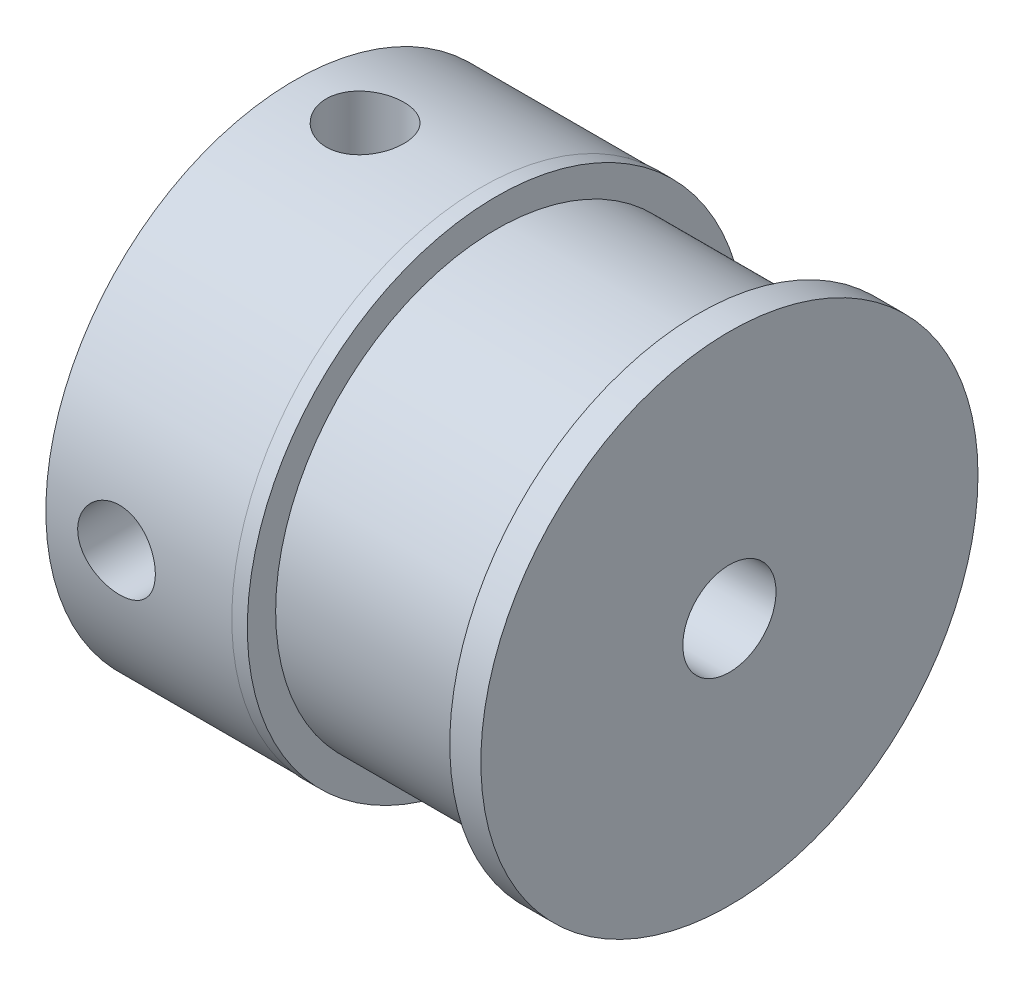
SolidWorks part; units mm, degrees
material "6061-T6 (SS)"
ref_plane "Front Plane" through (0, 0, 0) normal (0, 0, 1) x (1, 0, 0)
ref_plane "Top Plane" through (0, 0, 0) normal (0, 1, 0) x (1, 0, 0)
ref_plane "Right Plane" through (0, 0, 0) normal (1, 0, 0) x (0, 0, -1)
sketch "Sketch1" plane through (0, 0, 0) normal (0, 0, 1) x (1, 0, 0)
  line L0 (1.4515, 1.5) -> (1.4515, 8)
  line L1 (7.4515, 8.0157) -> (7.9515, 8.0157)
  line L2 (7.9515, 8.0157) -> (7.9515, 7.104)
  line L3 (7.9515, 7.104) -> (14.4515, 7.104)
  line L4 (14.4515, 7.104) -> (14.4515, 8)
  line L5 (14.4515, 8) -> (15.4515, 8)
  line L6 (15.4515, 8) -> (15.4515, 1.5)
  line L7 (15.4515, 1.5) -> (1.4515, 1.5)
  line L8 (0, 0) -> (-7.6744, 0) construction
  line L9 (7.4515, 8.0157) -> (7.4515, 8)
  line L10 (7.4515, 8) -> (1.4515, 8)
  point P1 (7.4515, 9.4661)
  dimension "D1" = 6.5
  dimension "D2" = 6.5
  dimension "D3" = 1.5
  dimension "D5" = 14
  dimension "D6" = 1
revolve "Revolve1" add sketch "Sketch1" angle 360 about L8
hole_wizard "M3x0.5 Tapped Hole1" positions "Sketch3" profile "Sketch2" tap size "M3x0.5" standard "ANSI Metric"
sketch "Sketch3" plane through (0, 0, 0) normal (0, 1, 0) x (1, 0, 0)
  line L0 (0, 0) -> (7.4515, 0) construction
  line L2 (7.4515, 8) -> (7.4515, -8) construction
  point P8 (3.7257, 0)
sketch "Sketch2" plane through (3.7257, 0, 0) normal (1, 0, 0) x (0, 0, -1)
  line L0 (0, 0) -> (0, 8.0157)
  line L1 (0, 8.0157) -> (1.25, 8.0157)
  line L2 (1.25, 8.0157) -> (1.25, 0)
  line L5 (1.25, 0) -> (0, 0)
  line L11 (0, -6.35) -> (0, 107.95) construction
  dimension "Thread Major Dia." = 2.5
  dimension "Thru Tap Drill Depth" = 8.0157
hole_wizard "M3x0.5 Tapped Hole2" positions "Sketch5" profile "Sketch4" tap size "M3x0.5" standard "ANSI Metric"
sketch "Sketch5" plane through (0, 0, 0) normal (0, 0, 1) x (1, 0, 0)
  line L0 (0, 0) -> (7.4515, 0) construction
  line L2 (7.4515, 8.0157) -> (7.4515, -8.0157) construction
  point P7 (3.7257, 0)
sketch "Sketch4" plane through (3.7257, 0, 0) normal (1, 0, 0) x (0, 1, 0)
  line L0 (0, 0) -> (0, 8.0157)
  line L1 (0, 8.0157) -> (1.25, 8.0157)
  line L2 (1.25, 8.0157) -> (1.25, 0)
  line L5 (1.25, 0) -> (0, 0)
  line L11 (0, -6.35) -> (0, 107.95) construction
  dimension "Thread Major Dia." = 2.5
  dimension "Thru Tap Drill Depth" = 8.0157
